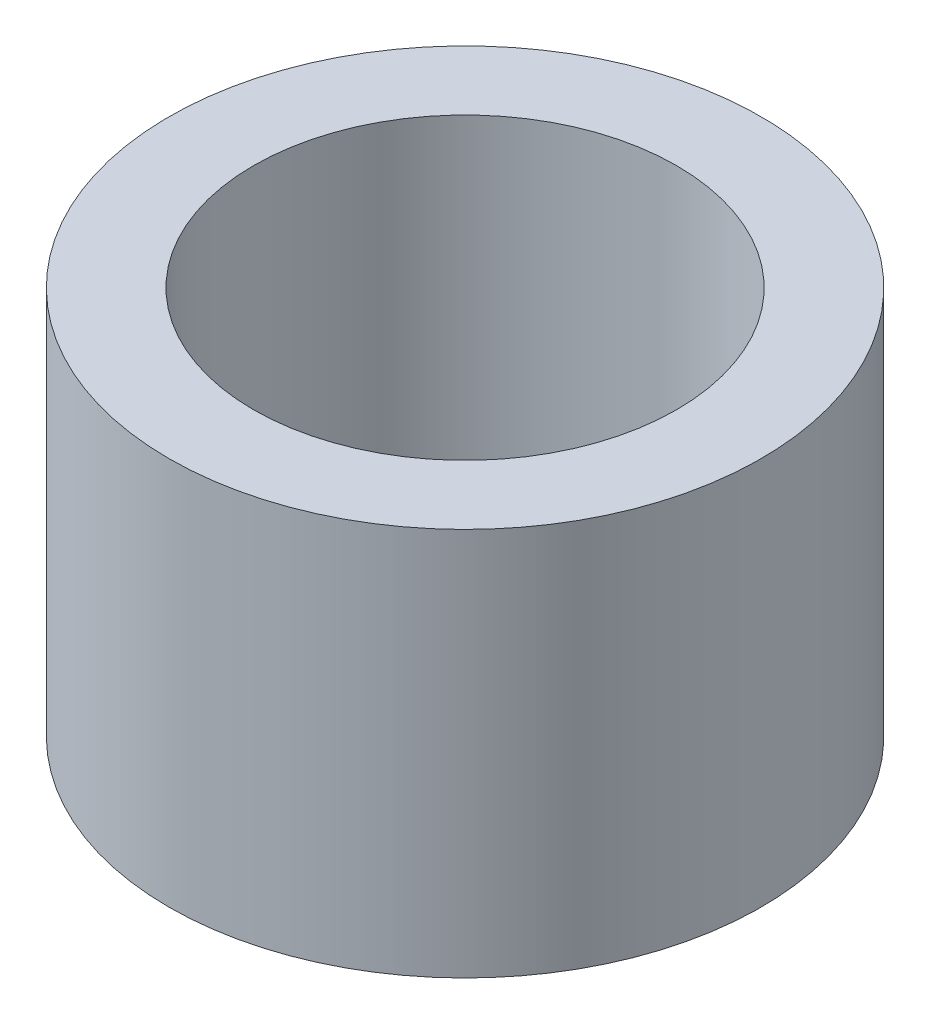
SolidWorks part; units mm, degrees
ref_plane "Front Plane" through (0, 0, 0) normal (0, 0, 1) x (1, 0, 0)
ref_plane "Top Plane" through (0, 0, 0) normal (0, 1, 0) x (1, 0, 0)
ref_plane "Right Plane" through (0, 0, 0) normal (1, 0, 0) x (0, 0, -1)
sketch "Sketch1" plane through (0, 0, 0) normal (0, 1, 0) x (1, 0, 0)
  circle A0 centre (0, 0) radius 7.9375
  circle A1 centre (0, 0) radius 11.1125
  dimension "D1" = 15.875
  dimension "D2" = 22.225
extrude "Boss-Extrude1" add sketch "Sketch1" along normal blind 14.5796
